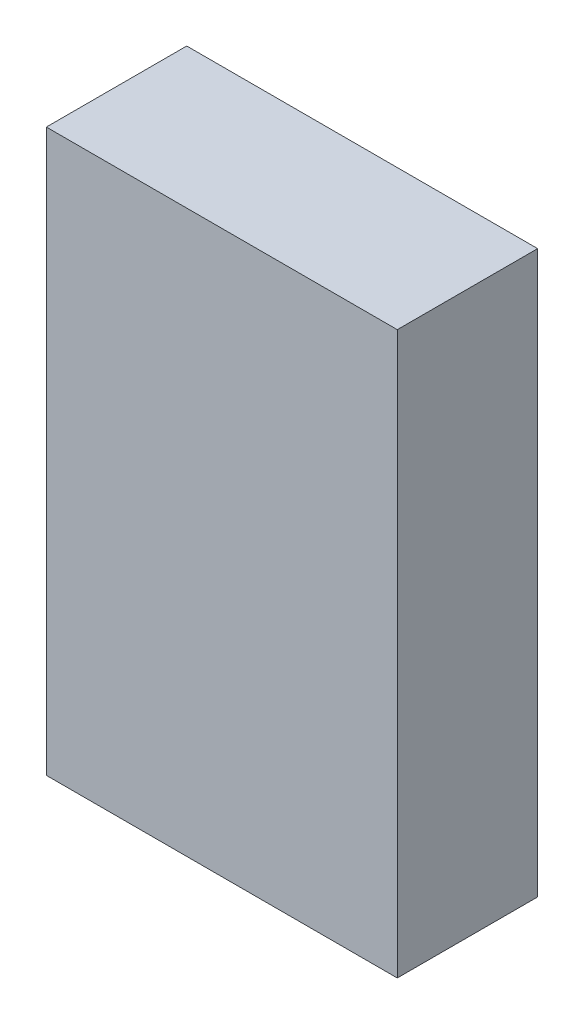
SolidWorks part; units mm, degrees
ref_plane "Front Plane" through (0, 0, 0) normal (0, 0, 1) x (1, 0, 0)
ref_plane "Top Plane" through (0, 0, 0) normal (0, 1, 0) x (1, 0, 0)
ref_plane "Right Plane" through (0, 0, 0) normal (1, 0, 0) x (0, 0, -1)
sketch "Sketch1" plane through (0, 0, 0) normal (0, 0, 1) x (1, 0, 0)
  line L1 (-7.9375, 12.7) -> (7.9375, 12.7)
  line L2 (-7.9375, 12.7) -> (-7.9375, -12.7)
  line L3 (-7.9375, -12.7) -> (7.9375, -12.7)
  line L4 (7.9375, 12.7) -> (7.9375, -12.7)
  line L5 (-7.9375, 12.7) -> (7.9375, -12.7) construction
  line L6 (-7.9375, -12.7) -> (7.9375, 12.7) construction
  point P0 (0, 0)
  dimension "D1" = 15.875
  dimension "D2" = 25.4
extrude "Boss-Extrude1" add sketch "Sketch1" along normal blind 6.35
sketch "Sketch2" plane through (0, 0, 6.35) normal (0, 0, 1) x (1, 0, 0)
  line L0 (1.5875, 7.1437) -> (1.5875, -7.1437) construction
  line L1 (1.5875, 0) -> (0, 0) construction
  line L2 (7.9375, 12.7) -> (-7.9375, 12.7) construction
  line L3 (7.9375, -12.7) -> (7.9375, 12.7) construction
  point P6 (1.5875, 7.1437)
  point P7 (1.5875, -7.1437)
  dimension "D1" = 14.2875
  dimension "D2" = 5.5562
  dimension "D3" = 19.8437
  dimension "D4" = 6.35
